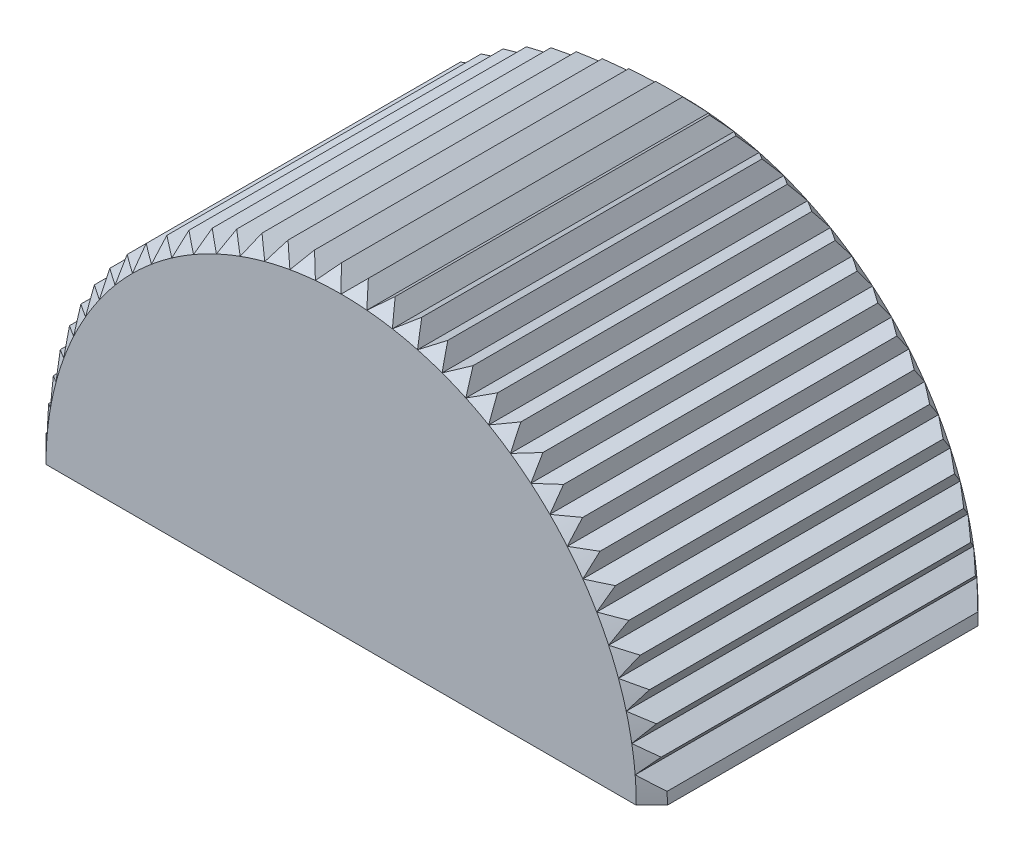
SolidWorks part; units mm, degrees
material "1.4000 (X6Cr13)"
ref_plane "Front Plane" through (0, 0, 0) normal (0, 0, 1) x (1, 0, 0)
ref_plane "Top Plane" through (0, 0, 0) normal (0, 1, 0) x (1, 0, 0)
ref_plane "Right Plane" through (0, 0, 0) normal (1, 0, 0) x (0, 0, -1)
sketch "Sketch1" plane through (0, 0, 0) normal (0, 0, 1) x (1, 0, 0)
  line L0 (-5, 0) -> (5, 0)
  arc A0 (5, 0) -> (-5, 0) centre (0, 0) ccw
  dimension "D1" = 10
extrude "Boss-Extrude1" add sketch "Sketch1" along normal blind 5.5
chamfer "Chamfer1" distance 0.25 angle 45 2 edges at (0, 5, 0) (0, 5, 5.5)
sketch "Sketch2" plane through (0, 0, 5.5) normal (0, 0, 1) x (1, 0, 0)
  line L0 (0, 0) -> (0, 5.9897) construction
  line L1 (0, 4.75) -> (0.244, 4.994)
  line L2 (0, 4.75) -> (-0.244, 4.994)
  arc A0 (5, 0) -> (-5, 0) centre (0, 0) ccw construction
  arc A1 (4.75, 0) -> (-4.75, 0) centre (0, 0) ccw construction
  arc A2 (-0.244, 4.994) -> (0.244, 4.994) centre (0, 0) cw
extrude "Cut-Extrude1" cut sketch "Sketch2" against normal through all
pattern_circular "CirPattern1" count 18 every 5 about axis through (0, 0, 0) along (0, 0, 1) of "Cut-Extrude1"
mirror "Mirror1" about plane through (0, 0, 0) normal (1, 0, 0) of "CirPattern1"
